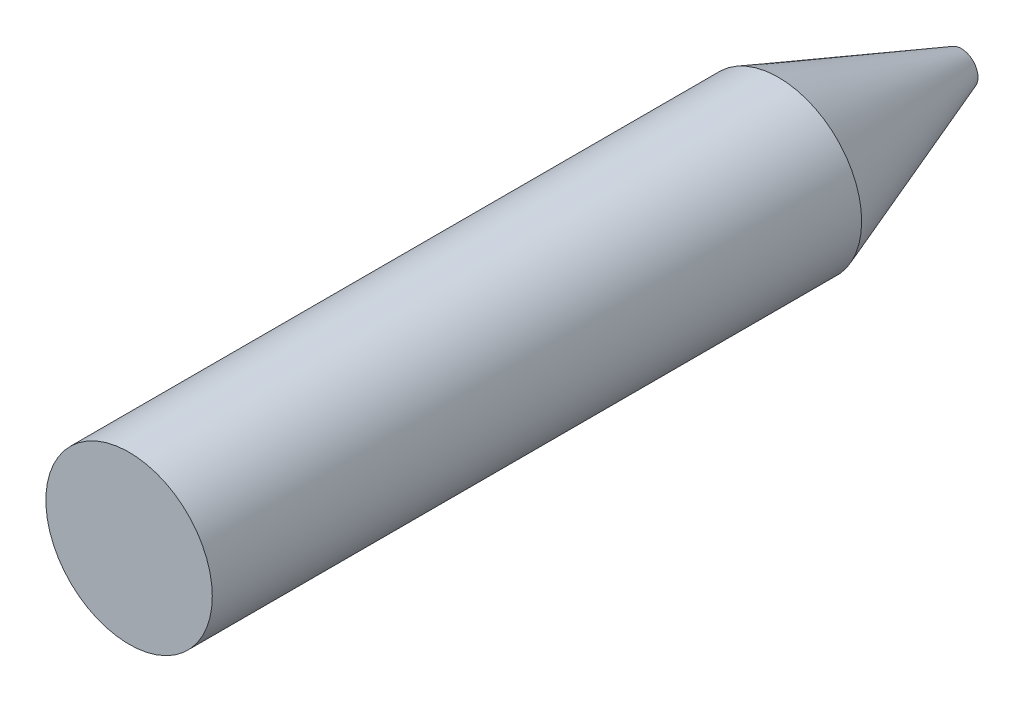
SolidWorks part; units mm, degrees
ref_plane "Front Plane" through (0, 0, 0) normal (0, 0, 1) x (1, 0, 0)
ref_plane "Top Plane" through (0, 0, 0) normal (0, 1, 0) x (1, 0, 0)
ref_plane "Right Plane" through (0, 0, 0) normal (1, 0, 0) x (0, 0, -1)
sketch "Sketch1" plane through (0, 0, 0) normal (0, 1, 0) x (1, 0, 0)
  line L0 (0, -68.6932) -> (0, 107.7398) construction
  line L1 (0, 0) -> (10, 0)
  line L2 (10, 0) -> (10, 78.0202)
  line L4 (0, 100) -> (0, 0)
  line L5 (10, 78.0202) -> (2, 100)
  line L6 (2, 100) -> (0, 100)
  point P8 (10, 83.4948)
  point P9 (6.0037, 100)
  dimension "D1" = 10
  dimension "D2" = 100
  dimension "D3" = 20
  dimension "D4" = 2
revolve "Revolve1" add sketch "Sketch1" angle 360 about L0
